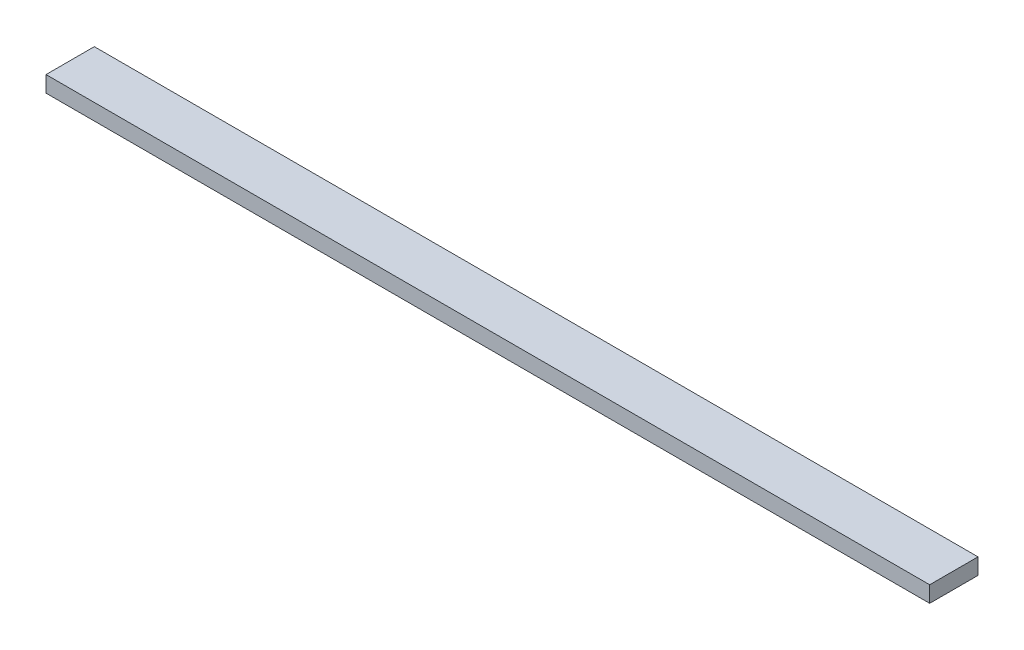
SolidWorks part; units mm, degrees
ref_plane "Front Plane" through (0, 0, 0) normal (0, 0, 1) x (1, 0, 0)
ref_plane "Top Plane" through (0, 0, 0) normal (0, 1, 0) x (1, 0, 0)
ref_plane "Right Plane" through (0, 0, 0) normal (1, 0, 0) x (0, 0, -1)
sketch "Sketch1" plane through (0, 0, 0) normal (0, 1, 0) x (1, 0, 0)
  line L0 (-274.265, 15) -> (274.265, -15) construction
  line L1 (-274.265, 15) -> (274.265, 15)
  line L2 (-274.265, 15) -> (-274.265, -15)
  line L3 (-274.265, -15) -> (274.265, -15)
  line L4 (274.265, 15) -> (274.265, -15)
  dimension "D1" = 548.53
  dimension "D2" = 30
extrude "Boss-Extrude1" add sketch "Sketch1" along normal blind 10
